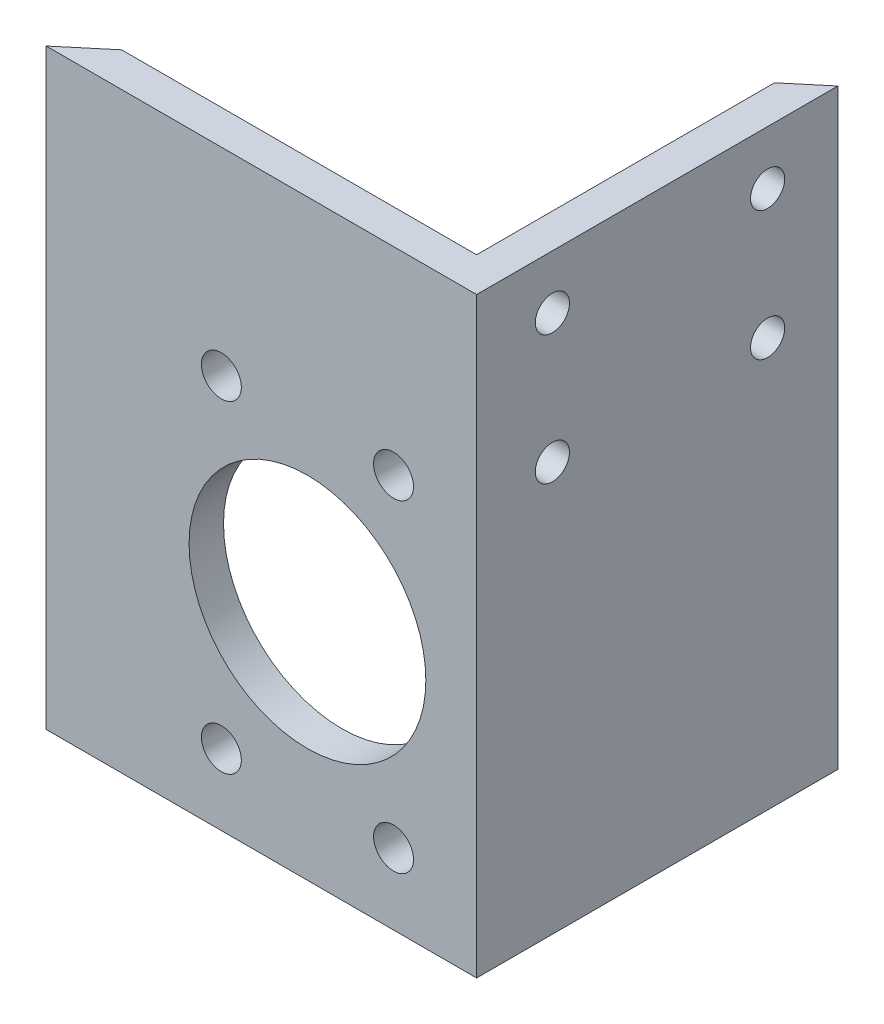
SolidWorks part; units mm, degrees
material "6061 Alloy"
ref_plane "Front Plane" through (0, 0, 0) normal (0, 0, 1) x (1, 0, 0)
ref_plane "Top Plane" through (0, 0, 0) normal (0, 1, 0) x (1, 0, 0)
ref_plane "Right Plane" through (0, 0, 0) normal (1, 0, 0) x (0, 0, -1)
sketch "Sketch1" plane through (0, 0, 0) normal (0, 1, 0) x (1, 0, 0)
  line L0 (0, 0) -> (0, 62.6783) construction
  line L1 (0, 0) -> (-46.1913, 55.0487) construction
  line L2 (0, 0) -> (38302.2222, 32139.3805) construction
  line L3 (0, 0) -> (50.8, 0)
  line L4 (50.8, 0) -> (50.8, 42.6263)
  line L5 (50.8, 42.6263) -> (46.736, 39.2162)
  line L6 (46.736, 39.2162) -> (46.736, 4.064)
  line L7 (46.736, 4.064) -> (4.8433, 4.064)
  line L8 (4.8433, 4.064) -> (0, 0)
  dimension "D1" = 40
  dimension "D2" = 4.064
  dimension "D3" = 4.064
  dimension "D4" = 50.8
extrude "Boss-Extrude1" add sketch "Sketch1" along normal blind 69.85
sketch "Sketch2" plane through (46.736, 0, 0) normal (-1, 0, 0) x (0, 0, 1)
  line L0 (-21.6401, 69.85) -> (-21.6401, 0) construction
  line L1 (-39.2162, 69.85) -> (-4.064, 69.85) construction
  line L2 (-39.2162, 0) -> (-4.064, 0) construction
  line L4 (-34.3401, 63.5) -> (-8.9401, 63.5) construction
  line L5 (-34.3401, 63.5) -> (-34.3401, 48.26) construction
  line L6 (-34.3401, 48.26) -> (-8.9401, 48.26) construction
  line L7 (-8.9401, 63.5) -> (-8.9401, 48.26) construction
  line L8 (-34.3401, 63.5) -> (-8.9401, 48.26) construction
  line L9 (-34.3401, 48.26) -> (-8.9401, 63.5) construction
  circle A0 centre (-34.3401, 63.5) radius 2.0193
  circle A1 centre (-8.9401, 63.5) radius 2.0193
  circle A2 centre (-8.9401, 48.26) radius 2.0193
  circle A3 centre (-34.3401, 48.26) radius 2.0193
  point P6 (-21.6401, 55.88)
  dimension "D3" = 4.0386
  dimension "D1" = 25.4
  dimension "D2" = 15.24
  dimension "D4" = 6.35
extrude "Cut-Extrude1" cut sketch "Sketch2" against normal through all
sketch "Sketch3" plane through (0, 0, -4.064) normal (0, 0, -1) x (-1, 0, 0)
  line L0 (-50.8, 69.85) -> (-50.8, 0) construction
  line L1 (-46.736, 46.2407) -> (-46.736, 50.2793) construction
  line L2 (-46.736, 46.2407) -> (-46.736, 50.2793) construction
  line L4 (-40.9956, 8.382) -> (-20.6756, 8.382) construction
  line L5 (-40.9956, 8.382) -> (-40.9956, 46.482) construction
  line L6 (-40.9956, 46.482) -> (-20.6756, 46.482) construction
  line L7 (-20.6756, 8.382) -> (-20.6756, 46.482) construction
  line L8 (-40.9956, 8.382) -> (-20.6756, 46.482) construction
  line L9 (-40.9956, 46.482) -> (-20.6756, 8.382) construction
  circle A0 centre (-30.8356, 27.432) radius 11.8999 construction
  circle A1 centre (-40.9956, 46.482) radius 2.3559
  circle A2 centre (-20.6756, 46.482) radius 2.3558
  circle A3 centre (-20.6756, 8.382) radius 2.3558
  circle A4 centre (-40.9956, 8.382) radius 2.3559
  circle A5 centre (-30.8356, 27.432) radius 13.97
  circle A6 centre (-30.8356, 27.432) radius 14.224 construction
  point P6 (-46.736, 48.26)
  dimension "D2" = 23.7998
  dimension "D4" = 4.7117
  dimension "D5" = 27.94
  dimension "D7" = 28.448
  dimension "D1" = 19.9644
  dimension "D3" = 20.828
  dimension "D6" = 20.32
  dimension "D8" = 38.1
extrude "Cut-Extrude2" cut sketch "Sketch3" against normal through all
sketch "Sketch4" plane through (0, 0, 0) normal (-0.6428, 0, -0.766) x (-0.766, 0, 0.6428)
  line L0 (-66.3147, 69.85) -> (0, 0) construction
  point P4 (-33.1573, 34.925)
ref_plane "Plane1" through (-16.3268, 0, -19.4575) normal (-0.6428, 0, -0.766) x (-0.766, 0, 0.6428)
sketch "Sketch7" plane through (-16.3268, 0, -19.4575) normal (-0.6428, 0, -0.766) x (-0.766, 0, 0.6428)
  line L0 (-33.1573, 34.925) -> (-33.1573, 69.85) construction
  line L1 (-66.3147, 69.85) -> (0, 0) construction
  line L2 (-38.4141, 69.85) -> (-6.3225, 69.85) construction
ref_plane "Center plane" through (25.4, 0, -21.3131) normal (0.766, 0, -0.6428) x (-0.6428, 0, -0.766)
ref_plane "Mech plate top" through (0, 12.7, 0) normal (0, -1, 0) x (-1, 0, 0)
